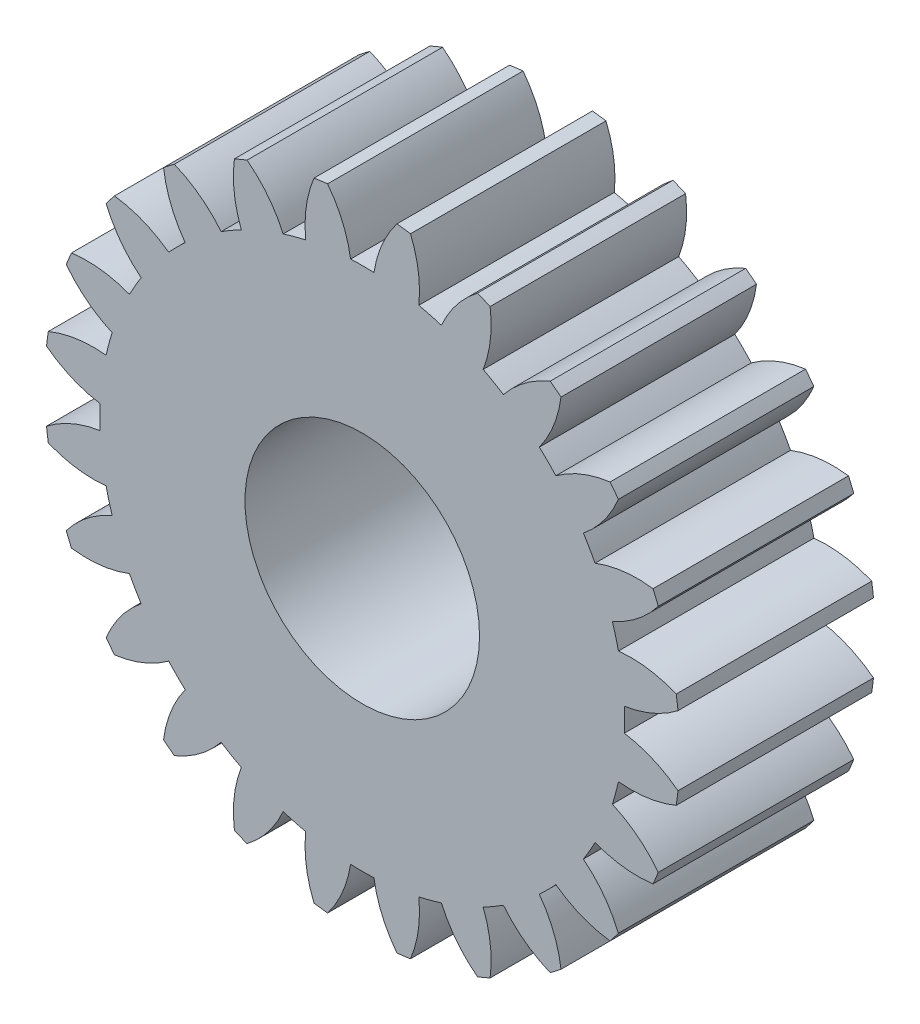
SolidWorks part; units mm, degrees
ref_plane "Front Plane" through (0, 0, 0) normal (0, 0, 1) x (1, 0, 0)
ref_plane "Top Plane" through (0, 0, 0) normal (0, 1, 0) x (1, 0, 0)
ref_plane "Right Plane" through (0, 0, 0) normal (1, 0, 0) x (0, 0, -1)
sketch "Sketch2" plane through (0, 0, 0) normal (0, 0, 1) x (1, 0, 0)
  arc A0 (-42.015, -22.9454) -> (-41.2685, -21.2015) centre (-45.034, -20.6212) ccw
  arc A1 (-41.2685, -21.2015) -> (-40.5096, -21.2015) centre (-40.889, -12.6882) ccw
  arc A2 (-40.5096, -21.2015) -> (-39.763, -22.9454) centre (-36.744, -20.6212) ccw
  arc A3 (-39.763, -22.9454) -> (-39.3219, -22.8873) centre (-40.889, -12.6882) ccw
  arc A4 (-39.3219, -22.8873) -> (-39.0521, -21.0096) centre (-42.8396, -21.4237) ccw
  arc A5 (-39.0521, -21.0096) -> (-38.3191, -20.8132) centre (-40.889, -12.6882) ccw
  arc A6 (-38.3191, -20.8132) -> (-37.1466, -22.3044) centre (-34.832, -19.2781) ccw
  arc A7 (-37.1466, -22.3044) -> (-36.7356, -22.1342) centre (-40.889, -12.6882) ccw
  arc A8 (-36.7356, -22.1342) -> (-36.961, -20.2507) centre (-40.5122, -21.6309) ccw
  arc A9 (-36.961, -20.2507) -> (-36.3038, -19.8712) centre (-40.889, -12.6882) ccw
  arc A10 (-36.3038, -19.8712) -> (-34.7853, -21.0082) centre (-33.3329, -17.4859) ccw
  arc A11 (-34.7853, -21.0082) -> (-34.4323, -20.7373) centre (-40.889, -12.6882) ccw
  arc A12 (-34.4323, -20.7373) -> (-35.1375, -18.9763) centre (-38.2105, -21.2286) ccw
  arc A13 (-35.1375, -18.9763) -> (-34.6009, -18.4397) centre (-40.889, -12.6882) ccw
  arc A14 (-34.6009, -18.4397) -> (-32.8399, -19.1449) centre (-32.3486, -15.3667) ccw
  arc A15 (-32.8399, -19.1449) -> (-32.5691, -18.792) centre (-40.889, -12.6882) ccw
  arc A16 (-32.5691, -18.792) -> (-33.706, -17.2735) centre (-36.0914, -20.2444) ccw
  arc A17 (-33.706, -17.2735) -> (-33.3266, -16.6162) centre (-40.889, -12.6882) ccw
  arc A18 (-33.3266, -16.6162) -> (-31.4431, -16.8416) centre (-31.9464, -13.065) ccw
  arc A19 (-31.4431, -16.8416) -> (-31.2728, -16.4306) centre (-40.889, -12.6882) ccw
  arc A20 (-31.2728, -16.4306) -> (-32.764, -15.2582) centre (-34.2992, -18.7452) ccw
  arc A21 (-32.764, -15.2582) -> (-32.5676, -14.5251) centre (-40.889, -12.6882) ccw
  arc A22 (-32.5676, -14.5251) -> (-30.6899, -14.2553) centre (-32.1536, -10.7377) ccw
  arc A23 (-30.6899, -14.2553) -> (-30.6319, -13.8143) centre (-40.889, -12.6882) ccw
  arc A24 (-30.6319, -13.8143) -> (-32.3758, -13.0677) centre (-32.9561, -16.8332) ccw
  arc A25 (-32.3758, -13.0677) -> (-32.3758, -12.3088) centre (-40.889, -12.6882) ccw
  arc A26 (-32.3758, -12.3088) -> (-30.6319, -11.5622) centre (-32.9561, -8.5432) ccw
  arc A27 (-30.6319, -11.5622) -> (-30.6899, -11.1211) centre (-40.889, -12.6882) ccw
  arc A28 (-30.6899, -11.1211) -> (-32.5676, -10.8514) centre (-32.1536, -14.6388) ccw
  arc A29 (-32.5676, -10.8514) -> (-32.764, -10.1183) centre (-40.889, -12.6882) ccw
  arc A30 (-32.764, -10.1183) -> (-31.2728, -8.9459) centre (-34.2992, -6.6313) ccw
  arc A31 (-31.2728, -8.9459) -> (-31.4431, -8.5348) centre (-40.889, -12.6882) ccw
  arc A32 (-31.4431, -8.5348) -> (-33.3266, -8.7602) centre (-31.9464, -12.3114) ccw
  arc A33 (-33.3266, -8.7602) -> (-33.706, -8.103) centre (-40.889, -12.6882) ccw
  arc A34 (-33.706, -8.103) -> (-32.5691, -6.5845) centre (-36.0914, -5.1321) ccw
  arc A35 (-32.5691, -6.5845) -> (-32.8399, -6.2316) centre (-40.889, -12.6882) ccw
  arc A36 (-32.8399, -6.2316) -> (-34.6009, -6.9368) centre (-32.3486, -10.0098) ccw
  arc A37 (-34.6009, -6.9368) -> (-35.1375, -6.4002) centre (-40.889, -12.6882) ccw
  arc A38 (-35.1375, -6.4002) -> (-34.4323, -4.6391) centre (-38.2105, -4.1478) ccw
  arc A39 (-34.4323, -4.6391) -> (-34.7853, -4.3683) centre (-40.889, -12.6882) ccw
  arc A40 (-34.7853, -4.3683) -> (-36.3038, -5.5053) centre (-33.3329, -7.8906) ccw
  arc A41 (-36.3038, -5.5053) -> (-36.961, -5.1258) centre (-40.889, -12.6882) ccw
  arc A42 (-36.961, -5.1258) -> (-36.7356, -3.2423) centre (-40.5122, -3.7456) ccw
  arc A43 (-36.7356, -3.2423) -> (-37.1466, -3.072) centre (-40.889, -12.6882) ccw
  arc A44 (-37.1466, -3.072) -> (-38.3191, -4.5633) centre (-34.832, -6.0984) ccw
  arc A45 (-38.3191, -4.5633) -> (-39.0521, -4.3669) centre (-40.889, -12.6882) ccw
  arc A46 (-39.0521, -4.3669) -> (-39.3219, -2.4892) centre (-42.8396, -3.9528) ccw
  arc A47 (-39.3219, -2.4892) -> (-39.763, -2.4311) centre (-40.889, -12.6882) ccw
  arc A48 (-39.763, -2.4311) -> (-40.5096, -4.175) centre (-36.744, -4.7553) ccw
  arc A49 (-40.5096, -4.175) -> (-41.2685, -4.175) centre (-40.889, -12.6882) ccw
  arc A50 (-41.2685, -4.175) -> (-42.015, -2.4311) centre (-45.034, -4.7553) ccw
  arc A51 (-42.015, -2.4311) -> (-42.4561, -2.4892) centre (-40.889, -12.6882) ccw
  arc A52 (-42.4561, -2.4892) -> (-42.7259, -4.3669) centre (-38.9384, -3.9528) ccw
  arc A53 (-42.7259, -4.3669) -> (-43.4589, -4.5633) centre (-40.889, -12.6882) ccw
  arc A54 (-43.4589, -4.5633) -> (-44.6314, -3.072) centre (-46.946, -6.0984) ccw
  arc A55 (-44.6314, -3.072) -> (-45.0424, -3.2423) centre (-40.889, -12.6882) ccw
  arc A56 (-45.0424, -3.2423) -> (-44.817, -5.1258) centre (-41.2658, -3.7456) ccw
  arc A57 (-44.817, -5.1258) -> (-45.4742, -5.5053) centre (-40.889, -12.6882) ccw
  arc A58 (-45.4742, -5.5053) -> (-46.9927, -4.3683) centre (-48.4452, -7.8906) ccw
  arc A59 (-46.9927, -4.3683) -> (-47.3457, -4.6391) centre (-40.889, -12.6882) ccw
  arc A60 (-47.3457, -4.6391) -> (-46.6405, -6.4002) centre (-43.5675, -4.1478) ccw
  arc A61 (-46.6405, -6.4002) -> (-47.1771, -6.9368) centre (-40.889, -12.6882) ccw
  arc A62 (-47.1771, -6.9368) -> (-48.9381, -6.2316) centre (-49.4294, -10.0098) ccw
  arc A63 (-48.9381, -6.2316) -> (-49.2089, -6.5845) centre (-40.889, -12.6882) ccw
  arc A64 (-49.2089, -6.5845) -> (-48.072, -8.103) centre (-45.6866, -5.1321) ccw
  arc A65 (-48.072, -8.103) -> (-48.4514, -8.7602) centre (-40.889, -12.6882) ccw
  arc A66 (-48.4514, -8.7602) -> (-50.3349, -8.5348) centre (-49.8316, -12.3114) ccw
  arc A67 (-50.3349, -8.5348) -> (-50.5052, -8.9459) centre (-40.889, -12.6882) ccw
  arc A68 (-50.5052, -8.9459) -> (-49.014, -10.1183) centre (-47.4788, -6.6313) ccw
  arc A69 (-49.014, -10.1183) -> (-49.2104, -10.8514) centre (-40.889, -12.6882) ccw
  arc A70 (-49.2104, -10.8514) -> (-51.0881, -11.1211) centre (-49.6245, -14.6388) ccw
  arc A71 (-51.0881, -11.1211) -> (-51.1461, -11.5622) centre (-40.889, -12.6882) ccw
  arc A72 (-51.1461, -11.5622) -> (-49.4023, -12.3088) centre (-48.822, -8.5432) ccw
  arc A73 (-49.4023, -12.3088) -> (-49.4023, -13.0677) centre (-40.889, -12.6882) ccw
  arc A74 (-49.4023, -13.0677) -> (-51.1461, -13.8143) centre (-48.822, -16.8332) ccw
  arc A75 (-51.1461, -13.8143) -> (-51.0881, -14.2553) centre (-40.889, -12.6882) ccw
  arc A76 (-51.0881, -14.2553) -> (-49.2104, -14.5251) centre (-49.6245, -10.7377) ccw
  arc A77 (-49.2104, -14.5251) -> (-49.014, -15.2582) centre (-40.889, -12.6882) ccw
  arc A78 (-49.014, -15.2582) -> (-50.5052, -16.4306) centre (-47.4788, -18.7452) ccw
  arc A79 (-50.5052, -16.4306) -> (-50.3349, -16.8416) centre (-40.889, -12.6882) ccw
  arc A80 (-50.3349, -16.8416) -> (-48.4514, -16.6162) centre (-49.8316, -13.065) ccw
  arc A81 (-48.4514, -16.6162) -> (-48.072, -17.2735) centre (-40.889, -12.6882) ccw
  arc A82 (-48.072, -17.2735) -> (-49.2089, -18.792) centre (-45.6866, -20.2444) ccw
  arc A83 (-49.2089, -18.792) -> (-48.9381, -19.1449) centre (-40.889, -12.6882) ccw
  arc A84 (-48.9381, -19.1449) -> (-47.1771, -18.4397) centre (-49.4294, -15.3667) ccw
  arc A85 (-47.1771, -18.4397) -> (-46.6405, -18.9763) centre (-40.889, -12.6882) ccw
  arc A86 (-46.6405, -18.9763) -> (-47.3457, -20.7373) centre (-43.5675, -21.2286) ccw
  arc A87 (-47.3457, -20.7373) -> (-46.9927, -21.0082) centre (-40.889, -12.6882) ccw
  arc A88 (-46.9927, -21.0082) -> (-45.4742, -19.8712) centre (-48.4452, -17.4859) ccw
  arc A89 (-45.4742, -19.8712) -> (-44.817, -20.2507) centre (-40.889, -12.6882) ccw
  arc A90 (-44.817, -20.2507) -> (-45.0424, -22.1342) centre (-41.2658, -21.6309) ccw
  arc A91 (-45.0424, -22.1342) -> (-44.6314, -22.3044) centre (-40.889, -12.6882) ccw
  arc A92 (-44.6314, -22.3044) -> (-43.4589, -20.8132) centre (-46.946, -19.2781) ccw
  arc A93 (-43.4589, -20.8132) -> (-42.7259, -21.0096) centre (-40.889, -12.6882) ccw
  arc A94 (-42.7259, -21.0096) -> (-42.4561, -22.8873) centre (-38.9384, -21.4237) ccw
  arc A95 (-42.4561, -22.8873) -> (-42.015, -22.9454) centre (-40.889, -12.6882) ccw
  circle A96 centre (-40.889, -12.6882) radius 3.81
  dimension "D1" = 20.6327
  dimension "D2" = 7.62
extrude "Boss-Extrude1" add sketch "Sketch2" along normal blind 6.35
